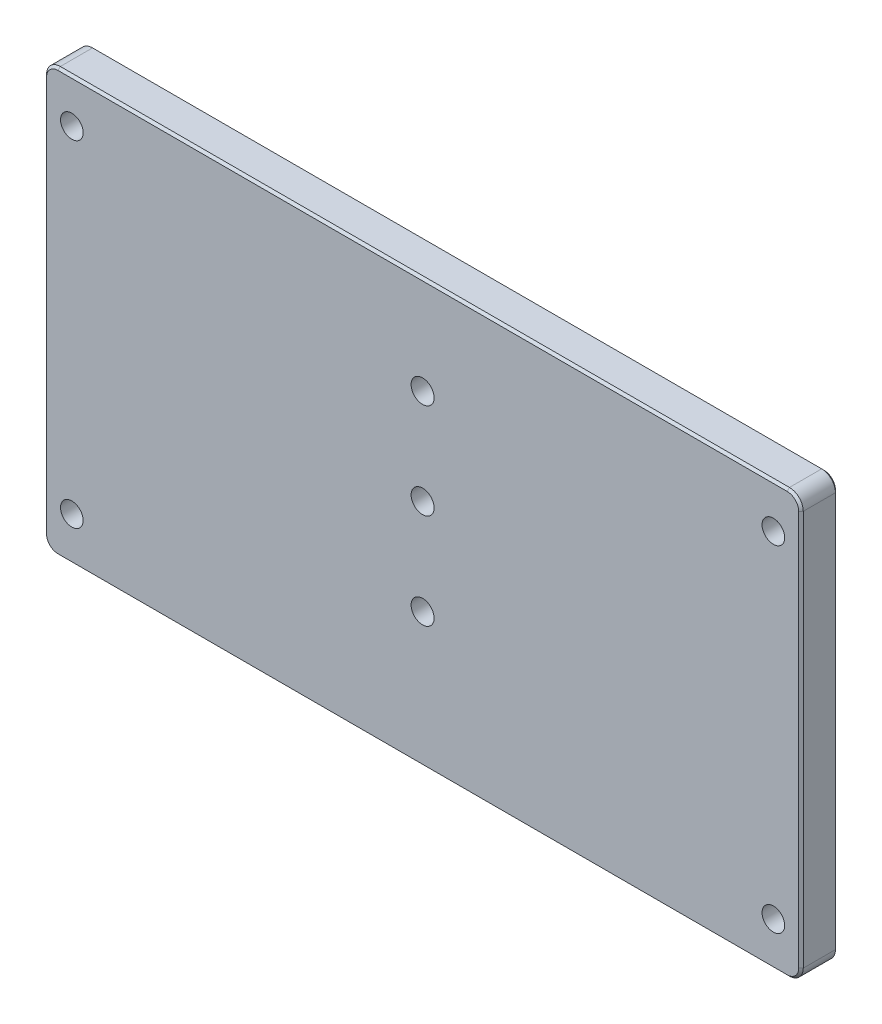
SolidWorks part; units mm, degrees
ref_plane "Front Plane" through (0, 0, 0) normal (0, 0, 1) x (1, 0, 0)
ref_plane "Top Plane" through (0, 0, 0) normal (0, 1, 0) x (1, 0, 0)
ref_plane "Right Plane" through (0, 0, 0) normal (1, 0, 0) x (0, 0, -1)
ref_plane "Plane1" through (0, 0, 3) normal (0, 0, 1) x (1, 0, 0)
sketch "Sketch1" plane through (0, 0, 3) normal (0, 0, 1) x (1, 0, 0)
  line L0 (-82.25, 46) -> (-82.25, -46)
  line L1 (-82.25, -46) -> (82.25, -46)
  line L2 (82.25, -46) -> (82.25, 46)
  line L3 (82.25, 46) -> (-82.25, 46)
extrude "Boss-Extrude1" add sketch "Sketch1" against normal blind 8
sketch "Sketch8" plane through (0, 0, 3) normal (0, 0, 1) x (1, 0, 0)
  line L0 (0, 46) -> (0, -46) construction
  line L3 (-82.25, 4) -> (82.25, 4) construction
  line L6 (82.25, 46) -> (-82.25, 46) construction
  line L7 (-82.25, -46) -> (82.25, -46) construction
  line L8 (-82.25, 46) -> (-82.25, -46) construction
  line L9 (82.25, -46) -> (82.25, 46) construction
  circle A0 centre (0, 24.75) radius 2.5
  circle A1 centre (0, 4) radius 2.5
  circle A2 centre (0, -16.75) radius 2.5
  dimension "D1" = 5
  dimension "D2" = 20.75
  dimension "D3" = 20.75
  dimension "D4" = 50
hole_wizard "Hole1" positions "Sketch3" profile "Sketch2" legacy end condition through all
sketch "Sketch3" plane through (0, 0, -5) normal (0, 0, -1) x (-1, 0, 0)
  point P0 (-76.25, -36.5)
  point P1 (76.25, 36.5)
sketch "Sketch2" plane through (76.25, -36.5, -5) normal (1, 0, 0) x (0, 1, 0)
  line L0 (0, 0) -> (0, 8)
  line L1 (0, 8) -> (2.4585, 8)
  line L2 (2.4585, 8) -> (2.4585, 0)
  line L3 (2.4585, 0) -> (0, 0)
  line L4 (0, 110) -> (0, -10) construction
  dimension "Diameter" = 4.917
  dimension "Depth" = 8
cosmetic thread "Cosmetic Thread4" parameters "D2"=6
cosmetic thread "Cosmetic Thread7" parameters "D2"=6
hole_wizard "Hole2" positions "Sketch5" profile "Sketch4" legacy end condition through all
sketch "Sketch5" plane through (0, 0, 3) normal (0, 0, 1) x (1, 0, 0)
  point P1 (-76.25, -36.5)
  point P2 (76.25, 36.5)
sketch "Sketch4" plane through (-76.25, -36.5, 3) normal (1, 0, 0) x (0, -1, 0)
  line L0 (0, 0) -> (0, 8)
  line L1 (0, 8) -> (2.4585, 8)
  line L2 (2.4585, 8) -> (2.4585, 0)
  line L3 (2.4585, 0) -> (0, 0)
  line L4 (0, 110) -> (0, -10) construction
  dimension "Diameter" = 4.917
  dimension "Depth" = 8
cosmetic thread "Cosmetic Thread5" parameters "D2"=6
cosmetic thread "Cosmetic Thread6" parameters "D2"=6
fillet "Fillet1" radius 3 4 edges at (-82.25, 46, -1) (82.25, 46, -1) (-82.25, -46, -1) (82.25, -46, -1)
chamfer "Chamfer2" distance 0.5 angle 45 16 edges at (82.25, 0, -5) (81.3713, -45.1213, -5) (81.3713, 45.1213, -5) (0, -46, -5) (0, 46, -5) (-81.3713, -45.1213, -5) (-81.3713, 45.1213, -5) (-82.25, 0, -5) (81.3713, 45.1213, 3) (0, 46, 3) (82.25, 0, 3) (-81.3713, 45.1213, 3) (81.3713, -45.1213, 3) (-82.25, 0, 3) (0, -46, 3) (-81.3713, -45.1213, 3)
hole_wizard "M6x1.0 Tapped Hole1" positions "Sketch9" profile "Sketch10" tap size "M6x1.0" standard "ANSI Metric" end condition through all
sketch "Sketch9" plane through (0, 0, 3) normal (0, 0, 1) x (1, 0, 0)
  point P0 (0, 24.75)
  point P3 (0, 4)
  point P6 (0, -16.75)
sketch "Sketch10" plane through (0, 24.75, 3) normal (1, 0, 0) x (0, -1, 0)
  line L0 (0, 0) -> (0, 8)
  line L1 (0, 8) -> (2.5, 8)
  line L2 (2.5, 8) -> (2.5, 0)
  line L5 (2.5, 0) -> (0, 0)
  line L11 (0, -6.35) -> (0, 107.95) construction
  dimension "Thread Major Dia." = 5
  dimension "Thru Tap Drill Depth" = 8
cosmetic thread "Cosmetic Thread1" parameters "D2"=6
cosmetic thread "Cosmetic Thread2" parameters "D2"=6
cosmetic thread "Cosmetic Thread3" parameters "D2"=6
